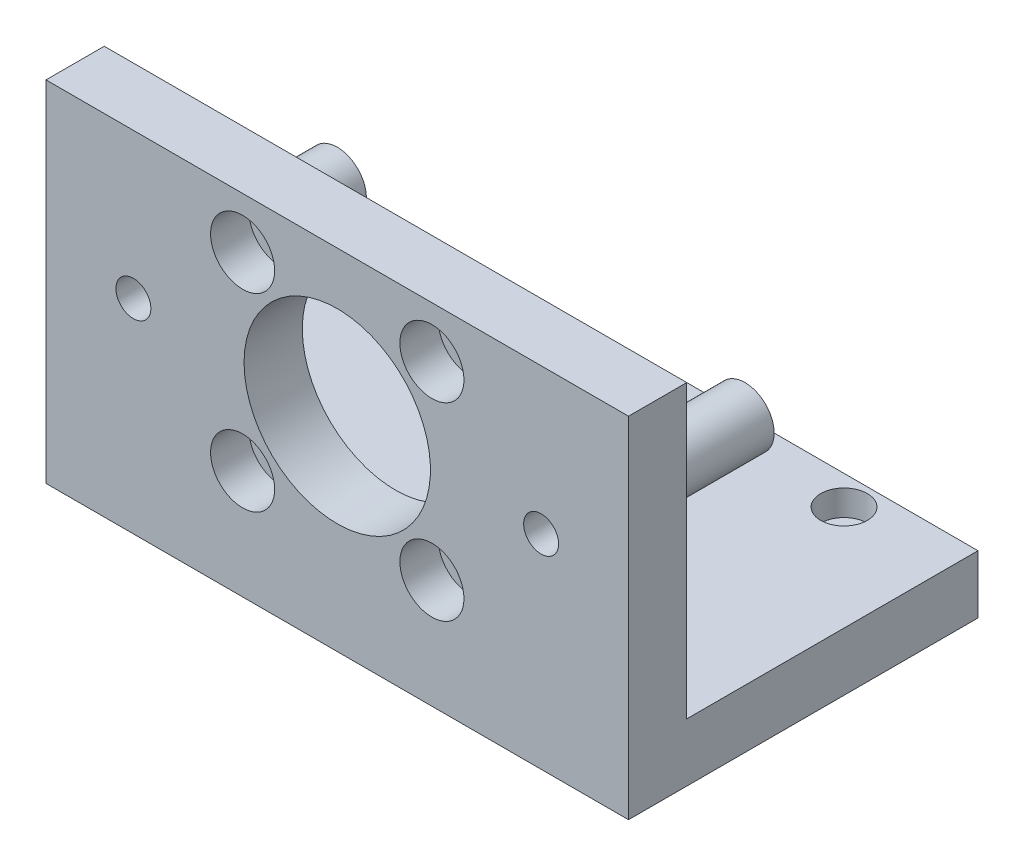
SolidWorks part; units mm, degrees
material "3003 Alloy"
ref_plane "Front Plane" through (0, 0, 0) normal (0, 0, 1) x (1, 0, 0)
ref_plane "Top Plane" through (0, 0, 0) normal (0, 1, 0) x (1, 0, 0)
ref_plane "Right Plane" through (0, 0, 0) normal (1, 0, 0) x (0, 0, -1)
sketch "Sketch1" plane through (0, 0, 0) normal (0, 1, 0) x (1, 0, 0)
  line L1 (-50, -25) -> (50, -25)
  line L2 (-50, -25) -> (-50, 25)
  line L3 (-50, 25) -> (50, 25)
  line L4 (50, -25) -> (50, 25)
  line L5 (-50, -25) -> (50, 25) construction
  line L6 (-50, 25) -> (50, -25) construction
  point P0 (0, 0)
  dimension "D1" = 100
  dimension "D2" = 50
extrude "Boss-Extrude1" add sketch "Sketch1" along normal blind 10
sketch "Sketch2" plane through (0, 10, 0) normal (0, 1, 0) x (1, 0, 0)
  line L0 (-32, 20) -> (32, 20) construction
  line L1 (32, 20) -> (32, -20) construction
  line L2 (32, -20) -> (-32, -20) construction
  line L3 (-32, -20) -> (-32, 20) construction
  circle A0 centre (32, 20) radius 2.25
  circle A1 centre (32, -20) radius 2.25
  circle A2 centre (-32, 20) radius 2.25
  circle A3 centre (-32, -20) radius 2.25
  point P5 (0, -20)
  point P10 (-32, 0)
  dimension "D1" = 4.5
  dimension "D2" = 40
  dimension "D3" = 64
extrude "Cut-Extrude1" cut sketch "Sketch2" against normal through all
sketch "Sketch3" plane through (0, 10, 0) normal (0, 1, 0) x (1, 0, 0)
  circle A0 centre (32, 20) radius 4
  circle A1 centre (32, -20) radius 4
  circle A2 centre (-32, 20) radius 4
  circle A3 centre (-32, -20) radius 4
  dimension "D1" = 8
  dimension "D2" = 8
extrude "Cut-Extrude2" cut sketch "Sketch3" against normal blind 4.4
sketch "Sketch4" plane through (0, 0, 25) normal (0, 0, 1) x (1, 0, 0)
  line L0 (-50, 10) -> (-50, 0) construction
  line L1 (-50, 0) -> (50, 0)
  line L2 (-50, 0) -> (-50, 60)
  line L3 (-50, 60) -> (50, 60)
  line L4 (50, 0) -> (50, 60)
  line L5 (-50, 0) -> (50, 0) construction
  dimension "D1" = 60
extrude "Boss-Extrude2" add sketch "Sketch4" along normal blind 10
sketch "Sketch5" plane through (0, 0, 25) normal (0, 0, -1) x (-1, 0, 0)
  line L0 (-50, 10) -> (-50, 60) construction
  circle A0 centre (0, 35) radius 16
  point P6 (-50, 35)
  dimension "D1" = 32
extrude "Cut-Extrude3" cut sketch "Sketch5" against normal through all
sketch "Sketch6" plane through (0, 0, 25) normal (0, 0, -1) x (-1, 0, 0)
  line L0 (-16.25, 51.25) -> (16.25, 51.25) construction
  line L1 (16.25, 51.25) -> (16.25, 18.75) construction
  line L2 (16.25, 18.75) -> (-16.25, 18.75) construction
  line L3 (-16.25, 18.75) -> (-16.25, 51.25) construction
  line L4 (50, 60) -> (50, 10) construction
  circle A0 centre (-16.25, 51.25) radius 3.3
  circle A1 centre (-16.25, 18.75) radius 3.3
  circle A2 centre (16.25, 18.75) radius 3.3
  circle A3 centre (16.25, 51.25) radius 3.3
  point P10 (50, 35)
  point P11 (16.25, 35)
  point P13 (0, 18.75)
  dimension "D1" = 6.6
  dimension "D2" = 32.5
  dimension "D3" = 32.5
extrude "Cut-Extrude4" cut sketch "Sketch6" against normal through all
sketch "Sketch7" plane through (0, 0, 35) normal (0, 0, 1) x (1, 0, 0)
  circle A0 centre (-16.25, 51.25) radius 5.5
  circle A1 centre (16.25, 51.25) radius 5.5
  circle A2 centre (16.25, 18.75) radius 5.5
  circle A3 centre (-16.25, 18.75) radius 5.5
  dimension "D1" = 11
extrude "Cut-Extrude5" cut sketch "Sketch7" against normal blind 6.6
sketch "Sketch8" plane through (0, 0, 25) normal (0, 0, -1) x (-1, 0, 0)
  line L0 (50, 60) -> (50, 10) construction
  circle A0 centre (-35, 35) radius 3
  circle A1 centre (35, 35) radius 3
  point P6 (50, 35)
  dimension "D1" = 6
  dimension "D2" = 35
  dimension "D3" = 35
extrude "Cut-Extrude6" cut sketch "Sketch8" against normal through all
sketch "Sketch9" plane through (0, 0, 25) normal (0, 0, -1) x (-1, 0, 0)
  circle A0 centre (-35, 35) radius 5
  circle A1 centre (-35, 35) radius 3
  circle A2 centre (35, 35) radius 5
  circle A3 centre (35, 35) radius 3
  dimension "D1" = 6
  dimension "D2" = 10
extrude "Boss-Extrude3" add sketch "Sketch9" along normal blind 25
